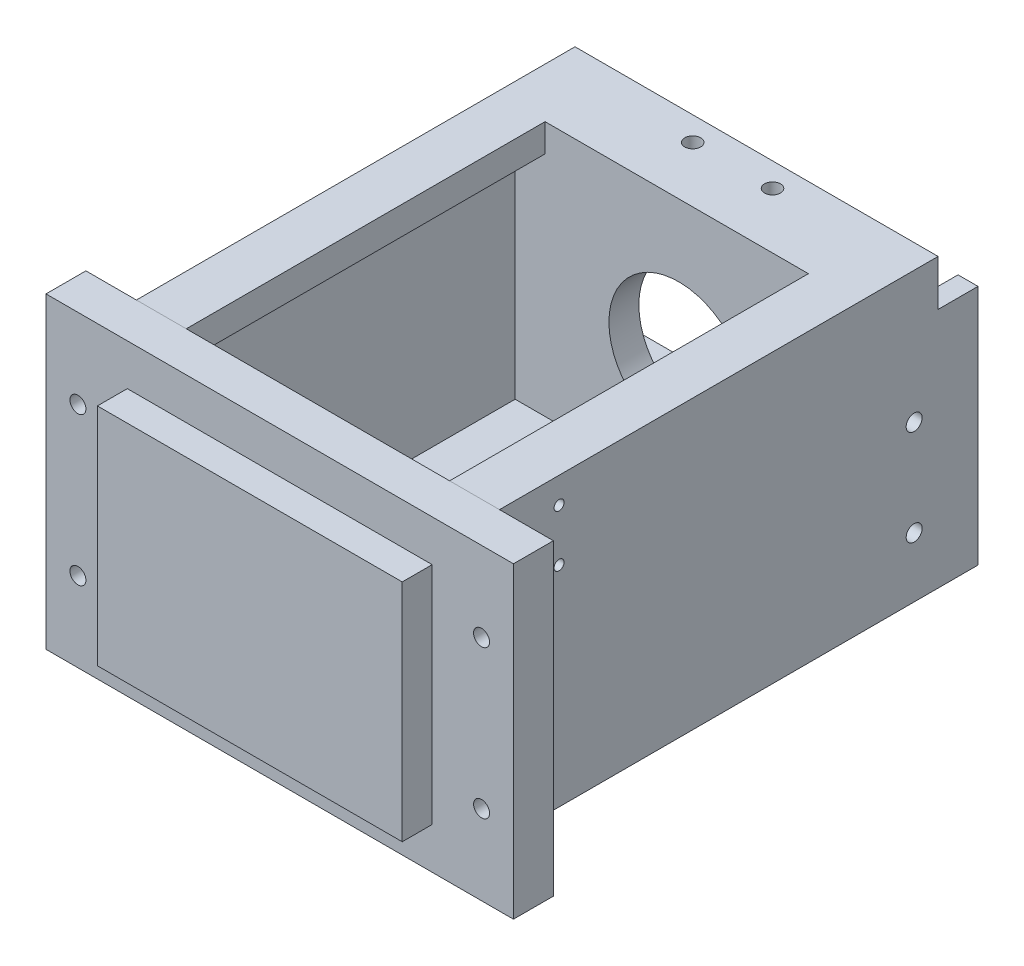
SolidWorks part; units mm, degrees
material "Ст 3 ГОСТ 380-88"
ref_plane "Front Plane" through (0, 0, 0) normal (0, 0, 1) x (1, 0, 0)
ref_plane "Top Plane" through (0, 0, 0) normal (0, 1, 0) x (1, 0, 0)
ref_plane "Right Plane" through (0, 0, 0) normal (1, 0, 0) x (0, 0, -1)
sketch "Sketch1" plane through (0, 0, 0) normal (0, 0, 1) x (1, 0, 0)
  line L1 (-25, -25.5) -> (25, -25.5)
  line L2 (-25, -25.5) -> (-25, 25.5)
  line L3 (-25, 25.5) -> (25, 25.5)
  line L4 (25, -25.5) -> (25, 25.5)
  line L5 (-25, -25.5) -> (25, 25.5) construction
  line L6 (-25, 25.5) -> (25, -25.5) construction
  point P0 (0, 0)
  dimension "D1" = 50
  dimension "D2" = 51
extrude "Boss-Extrude1" add sketch "Sketch1" along normal blind 3
sketch "Sketch2" plane through (0, 0, 3) normal (0, 0, 1) x (1, 0, 0)
  line L0 (25, -25.5) -> (25, 25.5) construction
  line L1 (-25, -25.5) -> (25, -25.5)
  line L2 (-25, -25.5) -> (-25, -22.5)
  line L3 (-25, -22.5) -> (25, -22.5)
  line L4 (25, -25.5) -> (25, -22.5)
  dimension "D1" = 3
extrude "Boss-Extrude2" add sketch "Sketch2" along normal blind 50
fillet "Fillet1" radius 2 2 edges at (0, -25.5, 0) (0, -22.5, 3)
chamfer "Chamfer1" distance 5 angle 45 4 edges at (-25, -24, 53) (25, -24, 53) (25, 25.5, 1.5) (-25, 25.5, 1.5)
sketch "Sketch4" plane through (0, 0, 3) normal (0, 0, 1) x (1, 0, 0)
  line L0 (20, 25.5) -> (-20, 25.5) construction
  circle A0 centre (0, 4.5) radius 12.55
  circle A1 centre (0, 4.5) radius 17.5 construction
  circle A2 centre (0, 22) radius 2.1
  circle A3 centre (0, -13) radius 2.1
  circle A4 centre (17.5, 4.5) radius 2.1
  circle A5 centre (-17.5, 4.5) radius 2.1
  dimension "D2" = 25.1
  dimension "D3" = 35
  dimension "D4" = 4.2
  dimension "D1" = 21
extrude "Cut-Extrude2" cut sketch "Sketch4" against normal blind 50
sketch "Sketch5" plane through (-25, 0, 0) normal (-1, 0, 0) x (0, 0, 1)
  line L0 (3, -2.5) -> (16, -22.5)
  line L1 (3, 20.5) -> (3, -20.5) construction
  line L2 (48, -22.5) -> (5, -22.5) construction
  line L3 (16, -22.5) -> (5, -22.5)
  line L4 (3, -20.5) -> (3, -2.5)
  arc A0 (5, -22.5) -> (3, -20.5) centre (5, -20.5) cw
  dimension "D1" = 20
  dimension "D2" = 13
extrude "Boss-Extrude3" add sketch "Sketch5" against normal blind 3
mirror "Mirror1" about plane through (0, 0, 0) normal (1, 0, 0) of "Boss-Extrude3"
ref_plane "Plano1" through (0, 0, 55) normal (0, 0, -1) x (-1, 0, 0)
sketch "Croquis1" plane through (0, 0, 55) normal (0, 0, -1) x (-1, 0, 0)
  line L1 (58.58, -38.575) -> (-58.575, -38.575)
  line L2 (58.58, -38.575) -> (58.58, 38.575)
  line L3 (58.58, 38.575) -> (-58.575, 38.575)
  line L4 (-58.575, -38.575) -> (-58.575, 38.575)
  dimension "D1" = 58.575
  dimension "D2" = 58.58
  dimension "D3" = 38.575
  dimension "D4" = 38.575
extrude "Saliente-Extruir1" add sketch "Croquis1" against normal blind 10 separate body
sketch "Croquis2" plane through (0, 0, 65) normal (0, 0, 1) x (1, 0, 0)
  line L1 (38.2, 28.2) -> (-38.2, 28.2)
  line L2 (38.2, 28.2) -> (38.2, -28.2)
  line L3 (38.2, -28.2) -> (-38.2, -28.2)
  line L4 (-38.2, 28.2) -> (-38.2, -28.2)
  dimension "D1" = 28.2
  dimension "D2" = 28.2
  dimension "D3" = 38.2
  dimension "D4" = 38.2
extrude "Saliente-Extruir2" add sketch "Croquis2" along normal blind 7.5
sketch "Croquis3" plane through (0, 0, 55) normal (0, 0, -1) x (-1, 0, 0)
  line L0 (-58.575, -38.575) -> (58.58, -38.575) construction
  line L1 (58.58, -38.575) -> (58.58, 38.575) construction
  line L2 (58.58, 38.575) -> (-58.575, 38.575) construction
  circle A0 centre (50.58, -18.575) radius 2
  circle A1 centre (50.58, 18.575) radius 2
  dimension "D2" = 8
  dimension "D3" = 4
  dimension "D4" = 20
  dimension "D5" = 8
  dimension "D6" = 4
  dimension "D1" = 20
extrude "Cortar-Extruir1" cut sketch "Croquis3" against normal blind 27.5
mirror "Simetría1" about plane through (0, 0, 0) normal (1, 0, 0) of "Cortar-Extruir1"
sketch "Croquis4" plane through (0, 0, 55) normal (0, 0, -1) x (-1, 0, 0)
  line L1 (41, 31.5) -> (-38, 31.5)
  line L2 (41, 31.5) -> (41, -25.5)
  line L3 (41, -25.5) -> (-38, -25.5)
  line L4 (-38, 31.5) -> (-38, -25.5)
  line L5 (46, 38.5) -> (-45, 38.5)
  line L6 (46, 38.5) -> (46, -33.5)
  line L7 (46, -33.5) -> (-45, -33.5)
  line L8 (-45, 38.5) -> (-45, -33.5)
  dimension "D1" = 13.5752
  dimension "D2" = 41
  dimension "D3" = 31.5
  dimension "D4" = 25.5
  dimension "D5" = 8
  dimension "D6" = 5
  dimension "D7" = 7
  dimension "D8" = 7
extrude "Saliente-Extruir3" add sketch "Croquis4" along normal blind 120
sketch "Sketch3" plane through (0, -22.5, 0) normal (0, 1, 0) x (1, 0, 0)
  line L0 (-15, -38) -> (-15, -37.9) construction
  line L1 (-17.1, -38) -> (-17.1, -37.9)
  line L2 (-12.9, -38) -> (-12.9, -37.9)
  line L3 (15, -38) -> (15, -37.9) construction
  line L4 (12.9, -38) -> (12.9, -37.9)
  line L5 (17.1, -38) -> (17.1, -37.9)
  line L6 (20, -53) -> (-20, -53) construction
  line L7 (-15, -37.95) -> (15, -37.95) construction
  arc A0 (-17.1, -38) -> (-12.9, -38) centre (-15, -38) ccw
  arc A1 (-12.9, -37.9) -> (-17.1, -37.9) centre (-15, -37.9) ccw
  arc A2 (12.9, -38) -> (17.1, -38) centre (15, -38) ccw
  arc A3 (17.1, -37.9) -> (12.9, -37.9) centre (15, -37.9) ccw
  point P2 (-15, -37.95)
  point P7 (15, -37.95)
  point P18 (0, -37.95)
  dimension "D1" = 4.2
  dimension "D2" = 0.1
  dimension "D3" = 15
  dimension "D4" = 30
extrude "Cut-Extrude1" cut sketch "Sketch3" against normal blind 50
sketch "Croquis5" plane through (0, 38.5, 0) normal (0, 1, 0) x (1, 0, 0)
  line L0 (-46, 65) -> (-46, -55) construction
  line L1 (-33.5, -55) -> (32.5, -55)
  line L2 (-33.5, -55) -> (-33.5, 35)
  line L3 (-33.5, 35) -> (32.5, 35)
  line L4 (32.5, -55) -> (32.5, 35)
  line L5 (45, 65) -> (45, -55) construction
  line L6 (-58.58, -55) -> (58.575, -55) construction
  dimension "D1" = 12.5
  dimension "D2" = 12.5
  dimension "D3" = 0
  dimension "D4" = 90
extrude "Cortar-Extruir2" cut sketch "Croquis5" against normal blind 64
sketch "Croquis7" plane through (0, -33.5, 0) normal (0, -1, 0) x (1, 0, 0)
  circle A0 centre (15, 19.7538) radius 2.1
  circle A1 centre (-15, 19.7538) radius 2.1
  arc A2 (17.1, 38) -> (12.9, 38) centre (15, 38) ccw construction
  arc A3 (-12.9, 38) -> (-17.1, 38) centre (-15, 38) ccw construction
  arc A4 (-17.1, 37.9) -> (-12.9, 37.9) centre (-15, 37.9) ccw construction
  dimension "D1" = 4.2
  dimension "D2" = 4.2
  dimension "D4" = 18.2462
  dimension "D6" = 30
  dimension "D3" = 18.2462
  dimension "D5" = 30
extrude "Cortar-Extruir3" cut sketch "Croquis7" against normal blind 20
sketch "Croquis8" plane through (0, 38.5, 0) normal (0, 1, 0) x (1, 0, 0)
  line L0 (-46, 65) -> (45, 65) construction
  line L1 (-46, 65) -> (-46, -55) construction
  line L2 (45, 65) -> (45, -55) construction
  circle A0 centre (-10.5, 49) radius 2
  circle A1 centre (9.5, 49) radius 2
  dimension "D1" = 4
  dimension "D2" = 4
  dimension "D3" = 16
  dimension "D4" = 16
  dimension "D5" = 35.5
  dimension "D6" = 35.5
sketch "Croquis9" plane through (-46, 0, 0) normal (-1, 0, 0) x (0, 0, 1)
  line L0 (-65, -33.5) -> (-65, 38.5) construction
  line L1 (-65, -33.5) -> (55, -33.5) construction
  circle A0 centre (-49, -18.5) radius 2
  circle A1 centre (-49, 5.5) radius 2
  dimension "D5" = 4
  dimension "D6" = 4
  dimension "D1" = 16
  dimension "D2" = 16
  dimension "D3" = 15
  dimension "D4" = 24
extrude "Cortar-Extruir5" cut sketch "Croquis9" against normal blind 110
extrude "Cortar-Extruir6" cut sketch "Croquis8" against normal blind 120
ref_plane "Plano2" through (0, 0, -35) normal (0, 0, -1) x (-1, 0, 0)
sketch "Croquis10" plane through (0, 0, -35) normal (0, 0, -1) x (-1, 0, 0)
  line L0 (0, 0) -> (41, 0) construction
  line L1 (41, 0) -> (41, -25.5)
  line L2 (41, 0) -> (41, 31.5)
  line L3 (41, -25.5) -> (-40, -25.5)
  line L4 (-40, -25.5) -> (-40, 31.5)
  line L5 (-40, 31.5) -> (41, 31.5)
  line L6 (41, -25.5) -> (41, 31.5) construction
  circle A1 centre (0, 3) radius 17.5
  dimension "D5" = 35
  dimension "D7" = 41
  dimension "D1" = 41
  dimension "D2" = 25.5
  dimension "D3" = 31.5
  dimension "D4" = 81
  dimension "D6" = 3
extrude "Saliente-Extruir4" add sketch "Croquis10" along normal blind 7.5
sketch "Croquis11" plane through (0, 38.5, 0) normal (0, 1, 0) x (1, 0, 0)
  line L0 (-41, 65) -> (-41, 55)
  line L1 (-41, 55) -> (40, 55)
  line L2 (40, 55) -> (40, 65)
  line L3 (40, 65) -> (-41, 65)
  line L4 (-46, 65) -> (-46, -55) construction
  line L5 (45, 65) -> (45, -55) construction
  line L6 (-46, 65) -> (45, 65) construction
  line L7 (-41, 55) -> (-46.9805, 55)
  line L8 (-46.9805, 55) -> (-46.9805, 65)
  line L9 (-46.9805, 65) -> (-41, 65)
  line L10 (40, 65) -> (45.913, 65)
  line L11 (45.913, 65) -> (45.913, 55)
  line L12 (45.913, 55) -> (40, 55)
  line M12 (45, -55) -> (45, 65)
  line M13 (45, 65) -> (-46, 65)
  line M14 (-46, 65) -> (-46, -55)
  dimension "D1" = 5
  dimension "D2" = 5
  dimension "D3" = 10
  dimension "D4" = 0
extrude "Cortar-Extruir7" cut sketch "Croquis11" against normal blind 7.9 contours L1 L2 L0 M13 | L7 L0 M13 M14 | L12 L2 M12 M13
sketch "Croquis12" plane through (0, 0, -42.5) normal (0, 0, -1) x (-1, 0, 0)
  line L0 (41, 31.5) -> (41, 27)
  line L1 (41, -25.5) -> (41, 31.5) construction
  line L2 (41, 27) -> (-38, 27)
  line L3 (-38, 31.5) -> (-38, -25.5) construction
  line L4 (-38, 27) -> (-38, 31.5)
  line L5 (-38, 31.5) -> (41, 31.5)
  dimension "D1" = 4.5
extrude "Saliente-Extruir5" add sketch "Croquis12" along normal blind 12.5
ref_plane "Plano3" through (-41, 30.6, -55) normal (0, 1, 0) x (1, 0, 0)
sketch "Croquis14" plane through (45, 0, 0) normal (1, 0, 0) x (0, 0, -1)
  line L0 (55, 30.6) -> (55, 27)
  line L1 (55, 27) -> (65, 27)
  line L2 (65, 30.6) -> (65, -33.5) construction
  line L3 (65, 27) -> (65, 30.6)
  line L4 (65, 30.6) -> (55, 30.6)
  dimension "D1" = 3.6
extrude "Cortar-Extruir8" cut sketch "Croquis14" against normal blind 100
sketch "Croquis21" plane through (45, 0, 0) normal (1, 0, 0) x (0, 0, -1)
  line L0 (55, 38.5) -> (-55, 38.5) construction
  line L1 (-55, 38.5) -> (-55, -33.5) construction
  circle A0 centre (-40, 32) radius 1.25
  circle A1 centre (-40, 19) radius 1.25
  dimension "D3" = 2.5
  dimension "D4" = 2.5
  dimension "D1" = 6.5
  dimension "D2" = 13
  dimension "D5" = 15
  dimension "D6" = 15
extrude "Cortar-Extruir10" cut sketch "Croquis21" against normal blind 4
sketch "Croquis22" plane through (0, -33.5, 0) normal (0, -1, 0) x (1, 0, 0)
  line L0 (45, -65) -> (45, 55) construction
  line L1 (45, -65) -> (-46, -65) construction
  circle A0 centre (30, -30) radius 1.5
  circle A1 centre (30, -20) radius 1.5
  dimension "D2" = 3
  dimension "D3" = 3
  dimension "D1" = 10
  dimension "D4" = 15
  dimension "D5" = 15
  dimension "D6" = 35
extrude "Cortar-Extruir11" cut sketch "Croquis22" against normal blind 40
sketch "Croquis23" plane through (-46, 0, 0) normal (-1, 0, 0) x (0, 0, 1)
  line L0 (55, 3.5) -> (45, 3.5)
  line L1 (55, -33.5) -> (55, 38.5) construction
  line L2 (45, 3.5) -> (45, 13.5)
  line L3 (45, 13.5) -> (55, 13.5)
  line L4 (55, 13.5) -> (55, 3.5)
  line L5 (-55, 38.5) -> (55, 38.5) construction
  dimension "D1" = 25
  dimension "D2" = 10
  dimension "D3" = 10
extrude "Cortar-Extruir12" cut sketch "Croquis23" against normal blind 10
sketch "Croquis24" plane through (0, 0, -65) normal (0, 0, -1) x (-1, 0, 0)
  line L0 (-38, -25.5) -> (-40, -25.5)
  line L1 (-40, -25.5) -> (-40, 27)
  line L2 (-38, 27) -> (-45, 27) construction
  line L3 (-40, 27) -> (-38, 27)
  line L4 (-38, 27) -> (-38, -25.5)
  dimension "D1" = 2
extrude "Cortar-Extruir13" cut sketch "Croquis24" against normal blind 22.5
